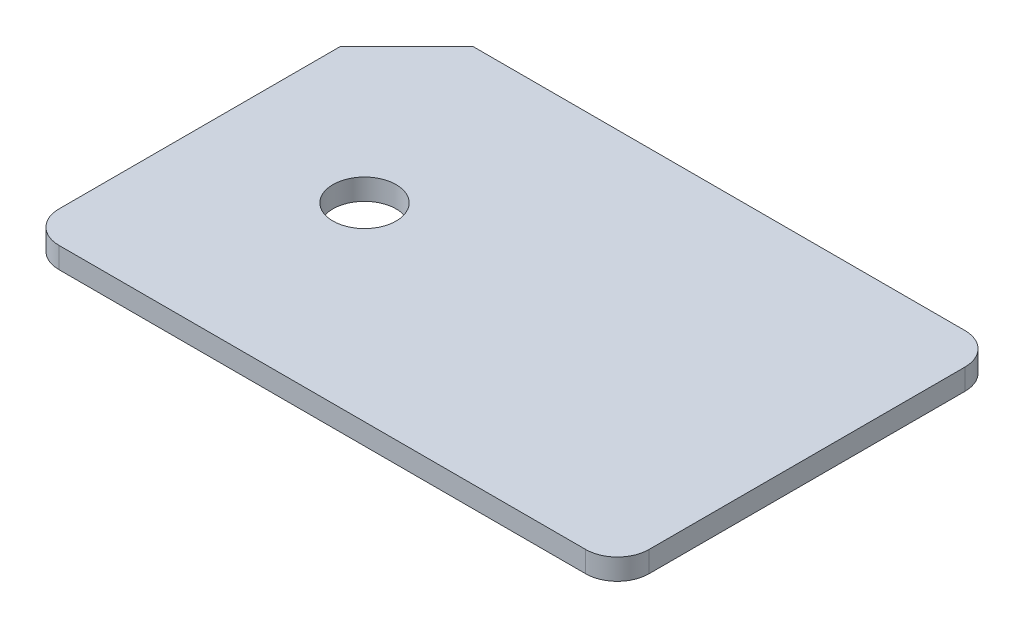
SolidWorks part; units mm, degrees
ref_plane "Front Plane" through (0, 0, 0) normal (0, 0, 1) x (1, 0, 0)
ref_plane "Top Plane" through (0, 0, 0) normal (0, 1, 0) x (1, 0, 0)
ref_plane "Right Plane" through (0, 0, 0) normal (1, 0, 0) x (0, 0, -1)
sketch "Sketch1" plane through (0, 0, 0) normal (0, 1, 0) x (1, 0, 0)
  line L0 (-56.6627, 29.5562) -> (-50.3343, 35.8846)
  line L1 (-50.3343, 35.8846) -> (-3.6627, 35.8846)
  line L2 (-0.6627, 32.8846) -> (-0.6627, 2.8846)
  line L3 (-3.6627, -0.1154) -> (-53.6627, -0.1154)
  line L4 (-56.6627, 2.8846) -> (-56.6627, 29.5562)
  arc A0 (-0.6627, 32.8846) -> (-3.6627, 35.8846) centre (-3.6627, 32.8846) ccw
  arc A1 (-56.6627, 2.8846) -> (-53.6627, -0.1154) centre (-53.6627, 2.8846) ccw
  arc A2 (-3.6627, -0.1154) -> (-0.6627, 2.8846) centre (-3.6627, 2.8846) ccw
extrude "Boss-Extrude1" add sketch "Sketch1" along normal blind 2
sketch "Sketch3" plane through (0, 2, 0) normal (0, 1, 0) x (1, 0, 0)
  line L0 (-50.3343, 35.8846) -> (-56.6627, 29.5562) construction
  line L1 (-56.6627, 35.8846) -> (-0.6627, 35.8846) construction
  line L2 (-28.6627, 35.8846) -> (-28.6627, -0.1154) construction
  line L3 (-53.6627, -0.1154) -> (-3.6627, -0.1154) construction
  line L4 (-28.6627, 17.8846) -> (-0.6627, 17.8846) construction
  line L5 (-0.6627, 2.8846) -> (-0.6627, 32.8846) construction
  line L6 (-28.6627, 17.8846) -> (-56.6627, 17.8846) construction
  line L7 (-56.6627, 29.5562) -> (-56.6627, 2.8846) construction
  circle A0 centre (-42.6627, 17.8846) radius 2.9996
extrude "Cut-Extrude1" cut sketch "Sketch3" against normal blind 2
